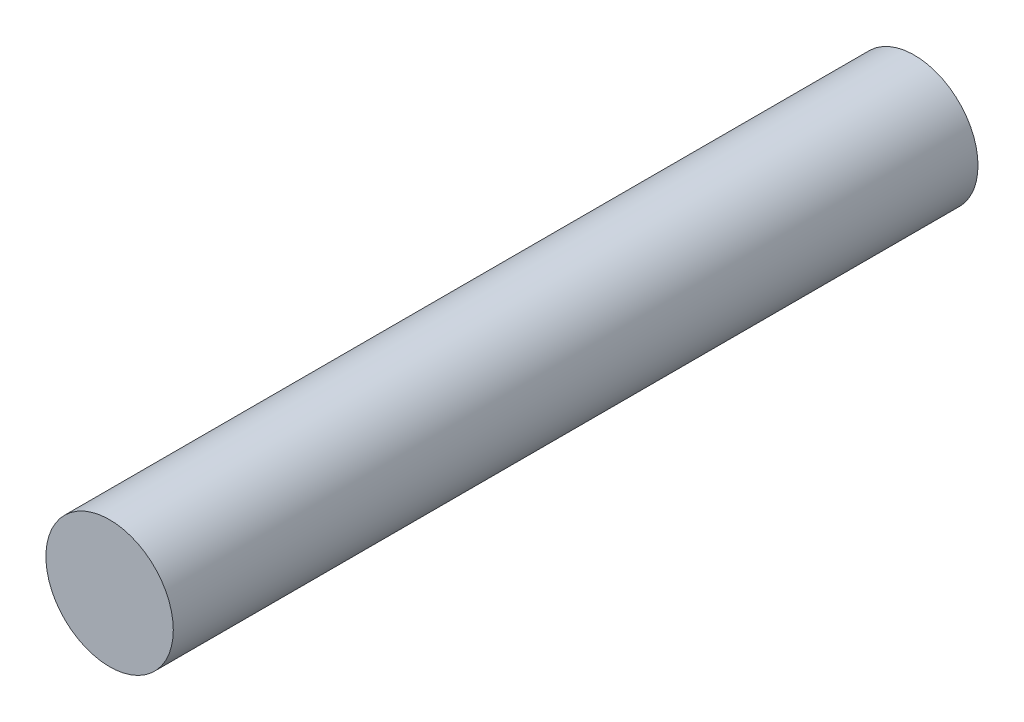
SolidWorks part; units mm, degrees
ref_plane "Front Plane" through (0, 0, 0) normal (0, 0, 1) x (1, 0, 0)
ref_plane "Top Plane" through (0, 0, 0) normal (0, 1, 0) x (1, 0, 0)
ref_plane "Right Plane" through (0, 0, 0) normal (1, 0, 0) x (0, 0, -1)
sketch "Sketch1" plane through (0, 0, 0) normal (0, 0, 1) x (1, 0, 0)
  circle A0 centre (-3.7427, -2.1521) radius 3.8
extrude "Boss-Extrude1" add sketch "Sketch1" along normal blind 48
